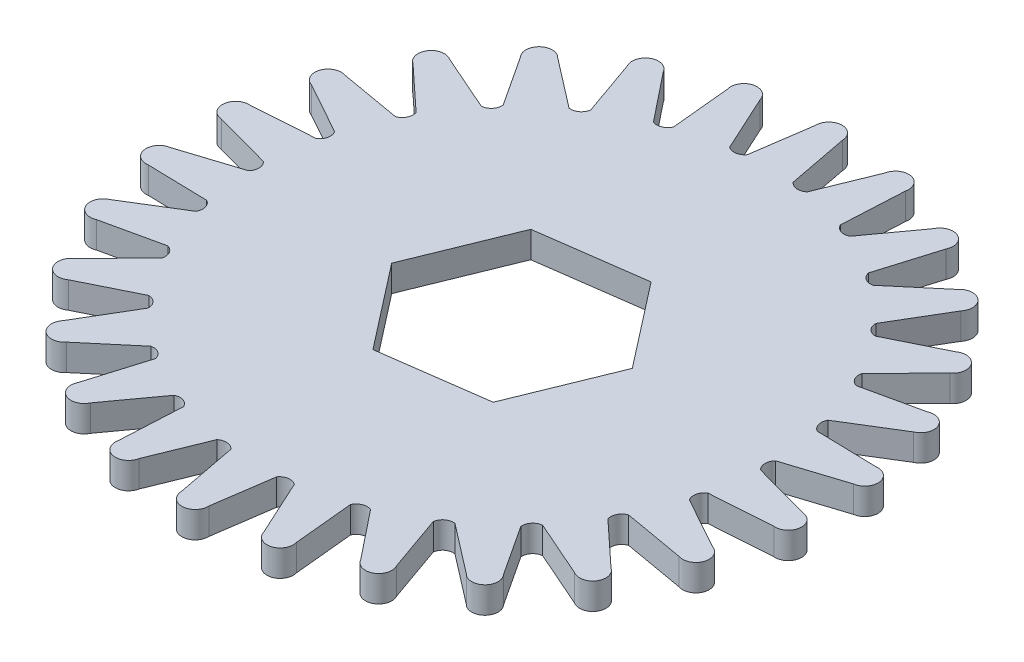
SolidWorks part; units mm, degrees
ref_plane "Спереди" through (0, 0, 0) normal (0, 0, 1) x (1, 0, 0)
ref_plane "Сверху" through (0, 0, 0) normal (0, 1, 0) x (1, 0, 0)
ref_plane "Справа" through (0, 0, 0) normal (1, 0, 0) x (0, 0, -1)
sketch "Эскиз1" plane through (0, 0, 0) normal (0, 1, 0) x (1, 0, 0)
  line L0 (-0.9991, 23.9577) -> (-1.6536, 19.4719)
  line L1 (4.9605, -6.3818) -> (8.007, 1.105)
  line L2 (8.007, 1.105) -> (3.0465, 7.4868)
  line L3 (3.0465, 7.4868) -> (-4.9605, 6.3818)
  line L4 (-4.9605, 6.3818) -> (-8.007, -1.105)
  line L5 (-8.007, -1.105) -> (-3.0465, -7.4868)
  line L6 (-3.0465, -7.4868) -> (4.9605, -6.3818)
  line L7 (0.9995, 24.0318) -> (1.8862, 19.4086)
  line L8 (4.7634, 23.5006) -> (3.0544, 19.3018)
  line L9 (6.7216, 23.0943) -> (6.4762, 18.3932)
  line L10 (10.249, 21.6778) -> (7.5849, 18.01)
  line L11 (12.0531, 20.8146) -> (10.6898, 16.3089)
  line L12 (15.139, 18.5951) -> (11.6745, 15.6715)
  line L13 (16.6841, 17.3252) -> (14.2821, 13.2768)
  line L14 (19.1492, 14.4318) -> (15.0857, 12.4222)
  line L15 (20.3455, 12.829) -> (17.0445, 9.473)
  line L16 (22.0465, 9.4297) -> (17.6202, 8.451)
  line L17 (22.8245, 7.5872) -> (18.8162, 5.1188)
  line L18 (23.6626, 3.8796) -> (19.1306, 3.9886)
  line L19 (23.977, 1.9045) -> (19.4945, 0.467)
  line L20 (23.9034, -1.896) -> (19.5293, -0.7056)
  line L21 (23.7361, -3.8889) -> (19.0397, -4.2119)
  line L22 (22.7551, -7.5613) -> (18.7929, -5.3587)
  line L23 (22.1157, -9.4563) -> (17.4785, -8.646)
  line L24 (20.2843, -12.7873) -> (16.9644, -9.7004)
  line L25 (19.21, -14.4742) -> (14.9015, -12.5777)
  line L26 (16.6347, -17.27) -> (14.15, -13.4784)
  line L27 (15.1879, -18.6508) -> (11.4585, -15.7783)
  line L28 (12.0183, -20.7492) -> (10.5132, -16.4731)
  line L29 (10.2831, -21.7436) -> (7.3495, -18.062)
  line L30 (6.7035, -23.0224) -> (6.2655, -18.5104)
  line L31 (4.7807, -23.5726) -> (2.8134, -19.296)
  line L32 (0.9991, -23.9577) -> (1.6536, -19.4719)
  line L33 (-0.9995, -24.0318) -> (-1.8862, -19.4086)
  line L34 (-4.7634, -23.5006) -> (-3.0544, -19.3018)
  line L35 (-6.7216, -23.0943) -> (-6.4762, -18.3932)
  line L36 (-10.249, -21.6778) -> (-7.5849, -18.01)
  line L37 (-12.0531, -20.8146) -> (-10.6898, -16.3089)
  line L38 (-15.139, -18.5951) -> (-11.6745, -15.6715)
  line L39 (-16.6841, -17.3252) -> (-14.2821, -13.2768)
  line L40 (-19.1492, -14.4318) -> (-15.0857, -12.4222)
  line L41 (-20.3455, -12.829) -> (-17.0445, -9.473)
  line L42 (-22.0465, -9.4297) -> (-17.6202, -8.451)
  line L43 (-22.8245, -7.5872) -> (-18.8162, -5.1188)
  line L44 (-23.6626, -3.8796) -> (-19.1306, -3.9886)
  line L45 (-23.977, -1.9045) -> (-19.4945, -0.467)
  line L46 (-23.9034, 1.896) -> (-19.5293, 0.7056)
  line L47 (-23.7361, 3.8889) -> (-19.0397, 4.2119)
  line L48 (-22.7551, 7.5613) -> (-18.7929, 5.3587)
  line L49 (-22.1157, 9.4563) -> (-17.4785, 8.646)
  line L50 (-20.2843, 12.7873) -> (-16.9644, 9.7004)
  line L51 (-19.21, 14.4742) -> (-14.9015, 12.5777)
  line L52 (-16.6347, 17.27) -> (-14.15, 13.4784)
  line L53 (-15.1879, 18.6508) -> (-11.4585, 15.7783)
  line L54 (-12.0183, 20.7492) -> (-10.5132, 16.4731)
  line L55 (-10.2831, 21.7436) -> (-7.3495, 18.062)
  line L56 (-6.7035, 23.0224) -> (-6.2655, 18.5104)
  line L57 (-4.7807, 23.5726) -> (-2.8134, 19.296)
  arc A1 (-0.9991, 23.9577) -> (0.9995, 24.0318) centre (0, 24) cw
  arc A2 (1.8862, 19.4086) -> (3.0544, 19.3018) centre (2.5232, 19.9343) ccw
  arc A3 (4.7634, 23.5006) -> (6.7216, 23.0943) centre (5.7436, 23.3026) cw
  arc A4 (6.4762, 18.3932) -> (7.5849, 18.01) centre (7.2205, 18.7512) ccw
  arc A5 (10.249, 21.6778) -> (12.0531, 20.8146) centre (11.1534, 21.2509) cw
  arc A6 (10.6898, 16.3089) -> (11.6745, 15.6715) centre (11.4981, 16.4783) ccw
  arc A7 (15.139, 18.5951) -> (16.6841, 17.3252) centre (15.9149, 17.9643) cw
  arc A8 (14.2821, 13.2768) -> (15.0857, 12.4222) centre (15.1075, 13.2478) ccw
  arc A9 (19.1492, 14.4318) -> (20.3455, 12.829) centre (19.7516, 13.6336) cw
  arc A10 (17.0445, 9.473) -> (17.6202, 8.451) centre (17.8389, 9.2474) ccw
  arc A11 (22.0465, 9.4297) -> (22.8245, 7.5872) centre (22.4404, 8.5105) cw
  arc A12 (18.8162, 5.1188) -> (19.1306, 3.9886) centre (19.5336, 4.7095) ccw
  arc A13 (23.6626, 3.8796) -> (23.977, 1.9045) centre (23.825, 2.8929) cw
  arc A14 (19.4945, 0.467) -> (19.5293, -0.7056) centre (20.0931, -0.102) ccw
  arc A15 (23.9034, -1.896) -> (23.7361, -3.8889) centre (23.825, -2.8929) cw
  arc A16 (19.0397, -4.2119) -> (18.7929, -5.3587) centre (19.4848, -4.9076) ccw
  arc A17 (22.7551, -7.5613) -> (22.1157, -9.4563) centre (22.4404, -8.5105) cw
  arc A18 (17.4785, -8.646) -> (16.9644, -9.7004) centre (17.7441, -9.4281) ccw
  arc A19 (20.2843, -12.7873) -> (19.21, -14.4742) centre (19.7516, -13.6336) cw
  arc A20 (14.9015, -12.5777) -> (14.15, -13.4784) centre (14.9722, -13.4005) ccw
  arc A21 (16.6347, -17.27) -> (15.1879, -18.6508) centre (15.9149, -17.9643) cw
  circle A23 centre (0, 0) radius 7 construction
  arc A24 (11.4585, -15.7783) -> (10.5132, -16.4731) centre (11.3302, -16.5942) ccw
  arc A25 (12.0183, -20.7492) -> (10.2831, -21.7436) centre (11.1534, -21.2509) cw
  arc A26 (7.3495, -18.062) -> (6.2655, -18.5104) centre (7.0297, -18.8235) ccw
  arc A27 (6.7035, -23.0224) -> (4.7807, -23.5726) centre (5.7436, -23.3026) cw
  arc A28 (2.8134, -19.296) -> (1.6536, -19.4719) centre (2.3207, -19.9589) ccw
  arc A29 (0.9991, -23.9577) -> (-0.9995, -24.0318) centre (0, -24) cw
  arc A30 (-1.8862, -19.4086) -> (-3.0544, -19.3018) centre (-2.5232, -19.9343) ccw
  arc A31 (-4.7634, -23.5006) -> (-6.7216, -23.0943) centre (-5.7436, -23.3026) cw
  arc A32 (-6.4762, -18.3932) -> (-7.5849, -18.01) centre (-7.2205, -18.7512) ccw
  arc A33 (-10.249, -21.6778) -> (-12.0531, -20.8146) centre (-11.1534, -21.2509) cw
  arc A34 (-10.6898, -16.3089) -> (-11.6745, -15.6715) centre (-11.4981, -16.4783) ccw
  arc A35 (-15.139, -18.5951) -> (-16.6841, -17.3252) centre (-15.9149, -17.9643) cw
  arc A36 (-14.2821, -13.2768) -> (-15.0857, -12.4222) centre (-15.1075, -13.2478) ccw
  arc A37 (-19.1492, -14.4318) -> (-20.3455, -12.829) centre (-19.7516, -13.6336) cw
  arc A38 (-17.0445, -9.473) -> (-17.6202, -8.451) centre (-17.8389, -9.2474) ccw
  arc A39 (-22.0465, -9.4297) -> (-22.8245, -7.5872) centre (-22.4404, -8.5105) cw
  arc A40 (-18.8162, -5.1188) -> (-19.1306, -3.9886) centre (-19.5336, -4.7095) ccw
  arc A41 (-23.6626, -3.8796) -> (-23.977, -1.9045) centre (-23.825, -2.8929) cw
  arc A42 (-19.4945, -0.467) -> (-19.5293, 0.7056) centre (-20.0931, 0.102) ccw
  arc A43 (-23.9034, 1.896) -> (-23.7361, 3.8889) centre (-23.825, 2.8929) cw
  arc A44 (-19.0397, 4.2119) -> (-18.7929, 5.3587) centre (-19.4848, 4.9076) ccw
  arc A45 (-22.7551, 7.5613) -> (-22.1157, 9.4563) centre (-22.4404, 8.5105) cw
  arc A46 (-17.4785, 8.646) -> (-16.9644, 9.7004) centre (-17.7441, 9.4281) ccw
  arc A47 (-20.2843, 12.7873) -> (-19.21, 14.4742) centre (-19.7516, 13.6336) cw
  arc A48 (-14.9015, 12.5777) -> (-14.15, 13.4784) centre (-14.9722, 13.4005) ccw
  arc A49 (-16.6347, 17.27) -> (-15.1879, 18.6508) centre (-15.9149, 17.9643) cw
  arc A50 (-11.4585, 15.7783) -> (-10.5132, 16.4731) centre (-11.3302, 16.5942) ccw
  arc A51 (-12.0183, 20.7492) -> (-10.2831, 21.7436) centre (-11.1534, 21.2509) cw
  arc A52 (-7.3495, 18.062) -> (-6.2655, 18.5104) centre (-7.0297, 18.8235) ccw
  arc A53 (-6.7035, 23.0224) -> (-4.7807, 23.5726) centre (-5.7436, 23.3026) cw
  arc A54 (-2.8134, 19.296) -> (-1.6536, 19.4719) centre (-2.3207, 19.9589) ccw
  point P3 (-1.4887, 21.3819)
  point P5 (3.6539, 21.2097)
  point P8 (0, 0)
  point P9 (0, 0)
  point P28 (1.5687, 20.9017)
  point P36 (3.5448, 20.3972)
  point P43 (1.7369, 20.1869)
  point P48 (-0.0095, 0.1609)
  point P52 (3.3451, 20.016)
  point P62 (-0.0895, -3.9047)
  point P85 (0.0038, 0.0336)
  point P197 (0, 0)
  dimension "D1" = 26
extrude "Бобышка-Вытянуть1" add sketch "Эскиз1" along normal blind 2
